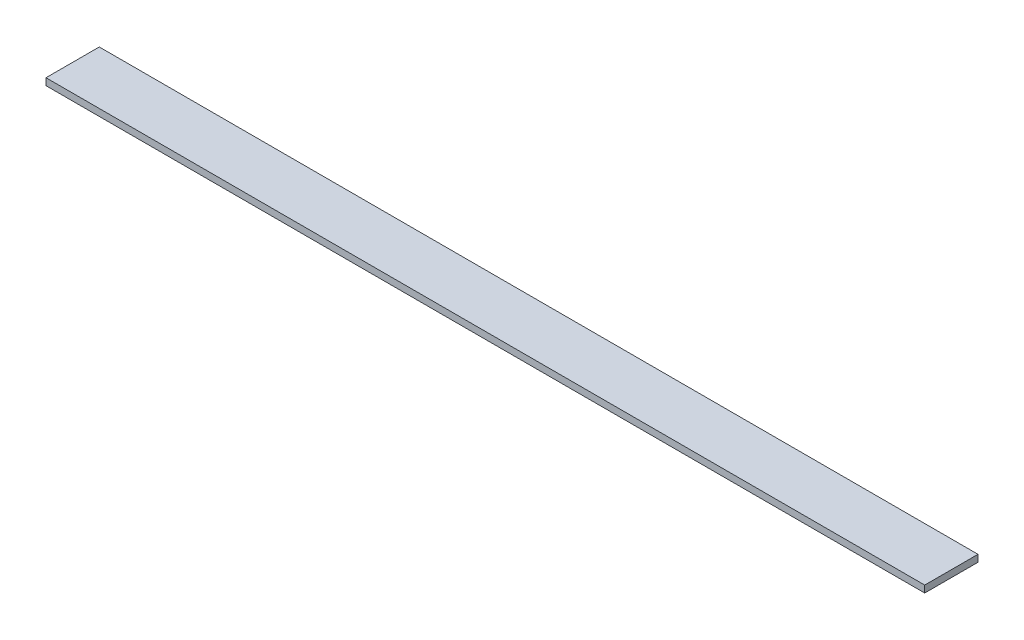
SolidWorks part; units mm, degrees
material "Plywood"
ref_plane "Front Plane" through (0, 0, 0) normal (0, 0, 1) x (1, 0, 0)
ref_plane "Top Plane" through (0, 0, 0) normal (0, 1, 0) x (1, 0, 0)
ref_plane "Right Plane" through (0, 0, 0) normal (1, 0, 0) x (0, 0, -1)
sketch "Sketch1" plane through (0, 0, 0) normal (1, 0, 0) x (0, 0, -1)
  line L0 (0, 0) -> (19.558, 0)
  line L1 (0, 0) -> (0, 2.54)
  line L2 (19.558, 0) -> (19.558, 2.54)
  line L3 (0, 2.54) -> (19.558, 2.54)
  dimension "D1" = 19.558
  dimension "D2" = 2.54
extrude "Boss-Extrude1" add sketch "Sketch1" along normal blind 322.58
